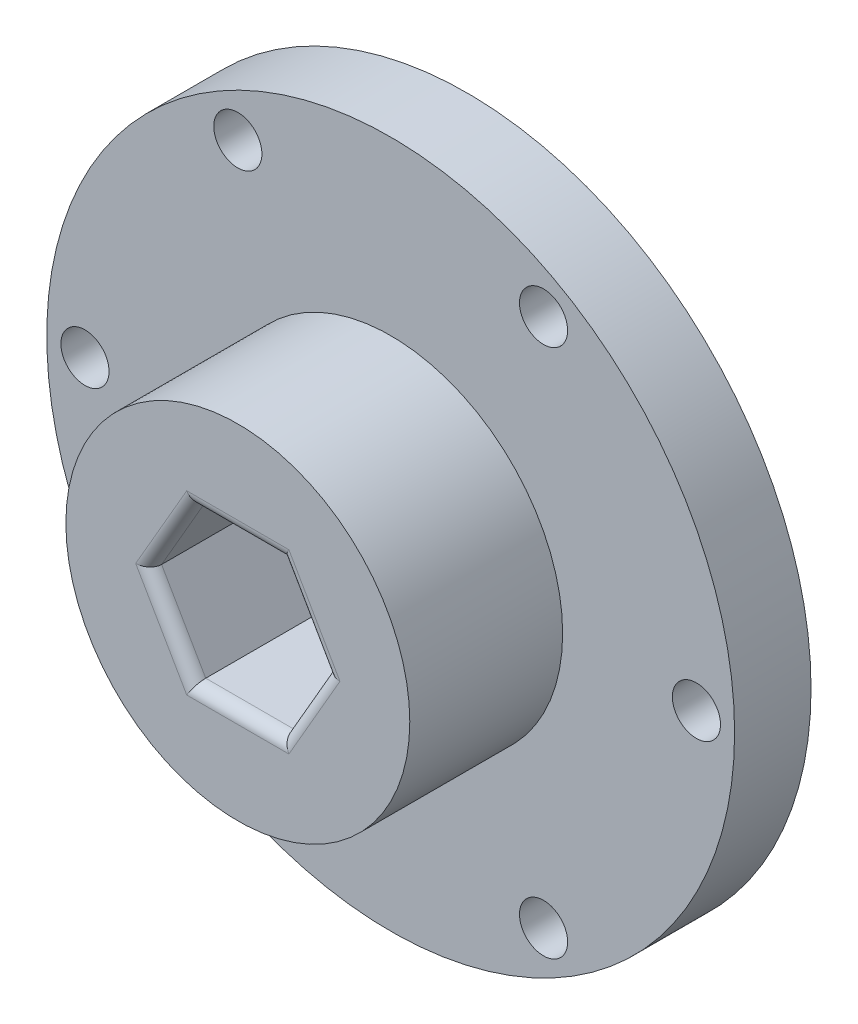
SolidWorks part; units mm, degrees
ref_plane "Front Plane" through (0, 0, 0) normal (0, 0, 1) x (1, 0, 0)
ref_plane "Top Plane" through (0, 0, 0) normal (0, 1, 0) x (1, 0, 0)
ref_plane "Right Plane" through (0, 0, 0) normal (1, 0, 0) x (0, 0, -1)
sketch "Sketch1" plane through (0, 0, 0) normal (0, 0, 1) x (1, 0, 0)
  circle A0 centre (0, 0) radius 28.575
  dimension "D1" = 57.15
extrude "Boss-Extrude1" add sketch "Sketch1" along normal blind 6.35
sketch "Sketch2" plane through (0, 0, 6.35) normal (0, 0, 1) x (1, 0, 0)
  circle A0 centre (0, 0) radius 14.2875
  dimension "D1" = 28.575
extrude "Boss-Extrude2" add sketch "Sketch2" along normal blind 12.7
sketch "Sketch3" plane through (0, 0, 19.05) normal (0, 0, 1) x (1, 0, 0)
  line L1 (7.3323, 0) -> (3.6662, 6.35)
  line L2 (3.6662, 6.35) -> (-3.6662, 6.35)
  line L3 (-3.6662, 6.35) -> (-7.3323, 0)
  line L4 (-7.3323, 0) -> (-3.6662, -6.35)
  line L5 (-3.6662, -6.35) -> (3.6662, -6.35)
  line L6 (3.6662, -6.35) -> (7.3323, 0)
  circle A0 centre (0, 0) radius 6.35 construction
  dimension "D1" = 12.7
extrude "Cut-Extrude1" cut sketch "Sketch3" against normal through all
sketch "Sketch4" plane through (0, 0, 6.35) normal (0, 0, 1) x (1, 0, 0)
  circle A0 centre (25.4, 0) radius 2
  circle A1 centre (0, 0) radius 28.575 construction
  circle A2 centre (12.7, -21.997) radius 2
  circle A3 centre (-12.7, -21.997) radius 2
  circle A4 centre (-25.4, 0) radius 2
  circle A5 centre (-12.7, 21.997) radius 2
  circle A6 centre (12.7, 21.997) radius 2
  point P19 (0, 0)
  dimension "D1" = 4
  dimension "D2" = 25.4
  dimension "D3" = 6
extrude "Cut-Extrude2" cut sketch "Sketch4" against normal through all
fillet "Fillet1" radius 1 6 edges at (0, 6.35, 19.05) (-5.4993, 3.175, 19.05) (-5.4993, -3.175, 19.05) (0, -6.35, 19.05) (5.4993, -3.175, 19.05) (5.4993, 3.175, 19.05)
